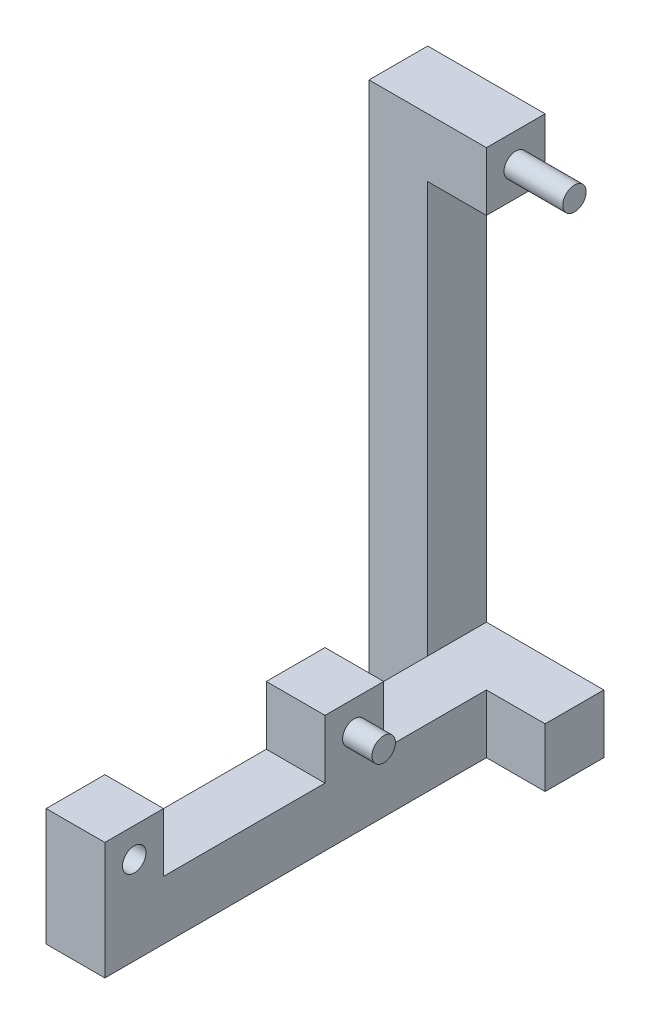
SolidWorks part; units mm, degrees
material "Galvanized Steel"
ref_plane "Front Plane" through (0, 0, 0) normal (0, 0, 1) x (1, 0, 0)
ref_plane "Top Plane" through (0, 0, 0) normal (0, 1, 0) x (1, 0, 0)
ref_plane "Right Plane" through (0, 0, 0) normal (1, 0, 0) x (0, 0, -1)
sketch "LowerBase" plane through (0, 0, 0) normal (1, 0, 0) x (0, 0, -1)
  line L9 (0, 0) -> (-1500, 0)
  line L10 (0, 0) -> (0, 200)
  line L11 (0, 200) -> (-1500, 200)
  line L12 (-1500, 0) -> (-1500, 200)
  line L13 (-1500, 200) -> (-1300, 200)
  line L14 (-1500, 200) -> (-1500, 400)
  line L15 (-1500, 400) -> (-1300, 400)
  line L16 (-1300, 200) -> (-1300, 400)
  line L17 (-750, 200) -> (-550, 200)
  line L18 (-750, 200) -> (-750, 400)
  line L19 (-750, 400) -> (-550, 400)
  line L20 (-550, 200) -> (-550, 400)
  dimension "D2" = 1500
  dimension "D1" = 200
  dimension "D3" = 200
  dimension "D4" = 200
  dimension "D5" = 200
  dimension "D6" = 200
  dimension "D7" = 550
  dimension "D8" = 550
extrude "Boss-Extrude1" add sketch "LowerBase" along normal blind 200 contours L12 L9 L10 L11 | L14 L15 L16 L13 | L19 L20 L17 L18
sketch "UpperBase" plane through (0, 0, 0) normal (1, 0, 0) x (0, 0, -1)
  line L1 (0, 0) -> (-200, 0)
  line L2 (0, 0) -> (0, 1800)
  line L3 (0, 1800) -> (-200, 1800)
  line L4 (-200, 0) -> (-200, 1800)
  dimension "D1" = 1800
  dimension "D2" = 200
extrude "Boss-Extrude2" add sketch "UpperBase" along direction (-1, 0, 0) on the side against the normal blind 200
sketch "TopPivot" plane through (0, 0, 0) normal (1, 0, 0) x (0, 0, -1)
  line L1 (-200, 1800) -> (0, 1800)
  line L2 (-200, 1800) -> (-200, 1600)
  line L3 (-200, 1600) -> (0, 1600)
  line L4 (0, 1800) -> (0, 1600)
  dimension "D1" = 200
  dimension "D2" = 200
extrude "Boss-Extrude3" add sketch "TopPivot" along normal blind 200
sketch "PressTable" plane through (0, 0, 0) normal (1, 0, 0) x (0, 0, -1)
  line L0 (0, 200) -> (-550, 200) construction
  line L1 (0, 0) -> (-200, 0)
  line L2 (0, 0) -> (0, 200)
  line L3 (0, 200) -> (-200, 200)
  line L4 (-200, 0) -> (-200, 200)
  dimension "D1" = 200
  dimension "D2" = 200
extrude "Boss-Extrude4" add sketch "PressTable" along normal blind 400
sketch "MiddleRivet" plane through (0, 0, 0) normal (1, 0, 0) x (0, 0, -1)
  line L0 (-750, 200) -> (-550, 400) construction
  circle A0 centre (-650, 300) radius 40
  dimension "D1" = 80
extrude "Boss-Extrude5" add sketch "MiddleRivet" along normal blind 300
sketch "TopRivet" plane through (0, 0, 0) normal (1, 0, 0) x (0, 0, -1)
  line L0 (0, 1800) -> (-200, 1600) construction
  circle A0 centre (-100, 1700) radius 40
  dimension "D1" = 80
extrude "Boss-Extrude6" add sketch "TopRivet" along normal blind 400 separate body
sketch "Sketch6" plane through (0, 0, 0) normal (1, 0, 0) x (0, 0, -1)
  line L0 (-1300, 400) -> (-1500, 200) construction
  line L1 (-1500, 0) -> (-1500, 400) construction
  circle A0 centre (-1400, 300) radius 40
  dimension "D1" = 80
extrude "Cut-Extrude1" cut sketch "Sketch6" against normal through all both and the other way through all
equation "\"baseFrameHeight\"= 180cm"
equation "\"baseFrameLength\"= 150cm"
equation "\"baseFrameThickness\"= 2 * \"RivetLength@PrintingPress.Assembly\""
equation "\"D2@LowerBase\" = \"baseFrameLength\""
equation "\"D1@LowerBase\" = \"baseFrameThickness\""
equation "\"D3@LowerBase\" = \"baseFrameThickness\""
equation "\"D4@LowerBase\" = \"baseFrameThickness\""
equation "\"D5@LowerBase\" = \"baseFrameThickness\""
equation "\"D6@LowerBase\" = \"baseFrameThickness\""
equation "\"D1@Boss-Extrude1\"=\"baseFrameThickness\""
equation "\"D1@UpperBase\" = \"baseFrameHeight\""
equation "\"D2@UpperBase\" = \"baseFrameThickness\""
equation "\"D1@Boss-Extrude2\"=\"baseFrameThickness\""
equation "\"D1@TopPivot\" = \"baseFrameThickness\""
equation "\"D2@TopPivot\" = \"baseFrameThickness\""
equation "\"D1@Boss-Extrude3\"=\"baseFrameThickness\""
equation "\"D2@PressTable\" = \"baseFrameThickness\""
equation "\"D1@Boss-Extrude4\"=2*\"baseFrameThickness\""
equation "\"D1@MiddleRivet\" = \"HoleMountDiameter@PrintingPress.Assembly\""
equation "\"D1@Boss-Extrude5\" = \"RivetLength@PrintingPress.Assembly\" + \"baseFrameThickness\""
equation "\"D1@TopRivet\" = \"HoleMountDiameter@PrintingPress.Assembly\""
equation "\"D1@Boss-Extrude6\"=2*\"RivetLength@PrintingPress.Assembly\" + \"baseFrameThickness\""
equation "\"D1@Sketch6\" = \"HoleMountDiameter@PrintingPress.Assembly\""
